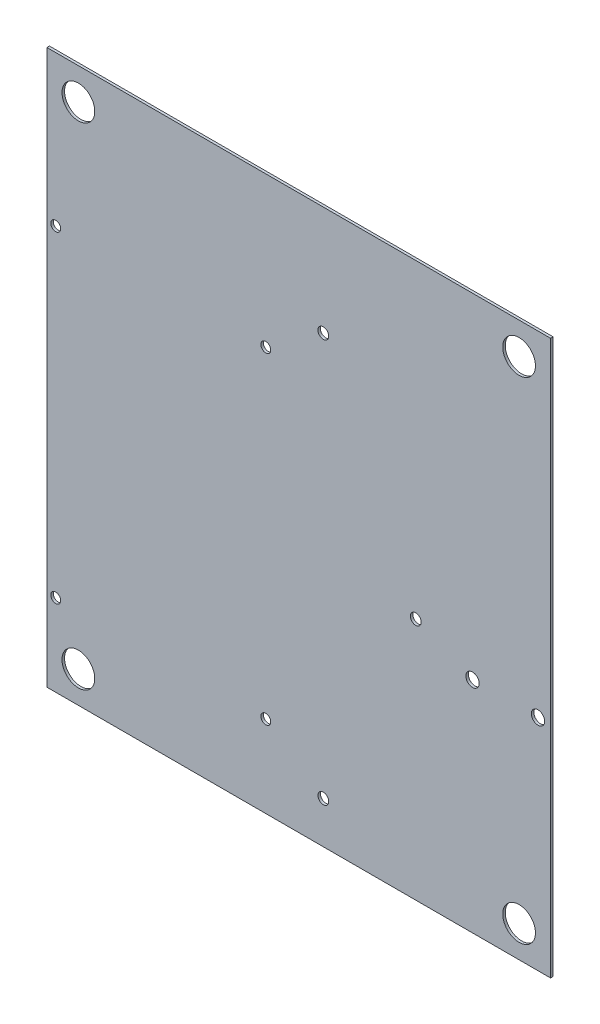
SolidWorks part; units mm, degrees
material "Plain Carbon Steel"
ref_plane "Front Plane" through (0, 0, 0) normal (0, 0, 1) x (1, 0, 0)
ref_plane "Top Plane" through (0, 0, 0) normal (0, 1, 0) x (1, 0, 0)
ref_plane "Right Plane" through (0, 0, 0) normal (1, 0, 0) x (0, 0, -1)
sketch "Sketch1" plane through (0, 0, 0) normal (0, 0, 1) x (1, 0, 0)
  line L0 (-87.5, 97.5) -> (-87.5, -97.5) construction
  line L1 (-100, 110) -> (100, 110)
  line L2 (-100, 110) -> (-100, -110)
  line L3 (-100, -110) -> (100, -110)
  line L4 (100, 110) -> (100, -110)
  line L5 (0, -110) -> (0, 110) construction
  line L6 (-100, 0) -> (100, 0) construction
  line L7 (-87.5, -97.5) -> (87.5, -97.5) construction
  line L8 (-96.495, 50.365) -> (-13.085, -77.495) construction
  line L9 (-4.58, 78.28) -> (52, 78.28) construction
  line L10 (-4.58, 78.28) -> (-4.58, -105) construction
  line L11 (-4.58, -105) -> (52, -105) construction
  line L12 (52, 78.28) -> (52, -105) construction
  line L13 (-100, 53.87) -> (-9.58, 53.87) construction
  line L14 (-100, 53.87) -> (-100, -81) construction
  line L15 (-100, -81) -> (-9.58, -81) construction
  line L16 (-9.58, 53.87) -> (-9.58, -81) construction
  line L17 (-54.79, 53.87) -> (-54.79, -81) construction
  line L19 (100, 39.2) -> (60, 39.2) construction
  line L20 (100, 39.2) -> (100, -86) construction
  line L21 (100, -86) -> (60, -86) construction
  line L22 (60, 39.2) -> (60, -86) construction
  circle A0 centre (-87.5, 97.5) radius 6.5
  circle A1 centre (87.5, 97.5) radius 6.5
  circle A2 centre (87.5, -97.5) radius 6.5
  circle A3 centre (-87.5, -97.5) radius 6.5
  circle A4 centre (9.76, -93.37) radius 2.1527
  circle A5 centre (9.76, 66.65) radius 2.1527
  circle A6 centre (46.46, -13.35) radius 2.1527
  circle A7 centre (-96.495, 50.365) radius 1.97
  circle A8 centre (-13.085, 50.365) radius 1.97
  circle A9 centre (-13.085, -77.495) radius 1.97
  circle A10 centre (-96.495, -77.495) radius 1.97
  circle A11 centre (69, -22.92) radius 2.65
  circle A12 centre (95, -22.92) radius 2.65
  point P0 (0, 0)
  point P12 (-87.5, 0)
  point P13 (0, -97.5)
  point P38 (-54.79, -13.565)
  point P39 (-54.79, -13.565)
  point P48 (0, 0)
  point P49 (0, 0)
  point P50 (0, 0)
  point P51 (-4.58, -106.1495)
  dimension "D5" = 13
  dimension "D9" = 4.3053
  dimension "D17" = 3.94
  dimension "D21" = 5.3
  dimension "D25" = 10
  dimension "D1" = 220
  dimension "D2" = 200
  dimension "D3" = 175
  dimension "D4" = 195
  dimension "D6" = 160.02
  dimension "D7" = 80
  dimension "D8" = 36.7
  dimension "D10" = 5.54
  dimension "D11" = 56.58
  dimension "D12" = 183.28
  dimension "D13" = 11.63
  dimension "D14" = 134.87
  dimension "D15" = 90.42
  dimension "D16" = 83.41
  dimension "D18" = 127.86
  dimension "D19" = 40
  dimension "D20" = 125.2
  dimension "D22" = 26
  dimension "D23" = 5
  dimension "D24" = 62.12
  dimension "D26" = 5
  dimension "D27" = 5
  dimension "D28" = 5
extrude "Boss-Extrude1" add sketch "Sketch1" along normal blind 1
